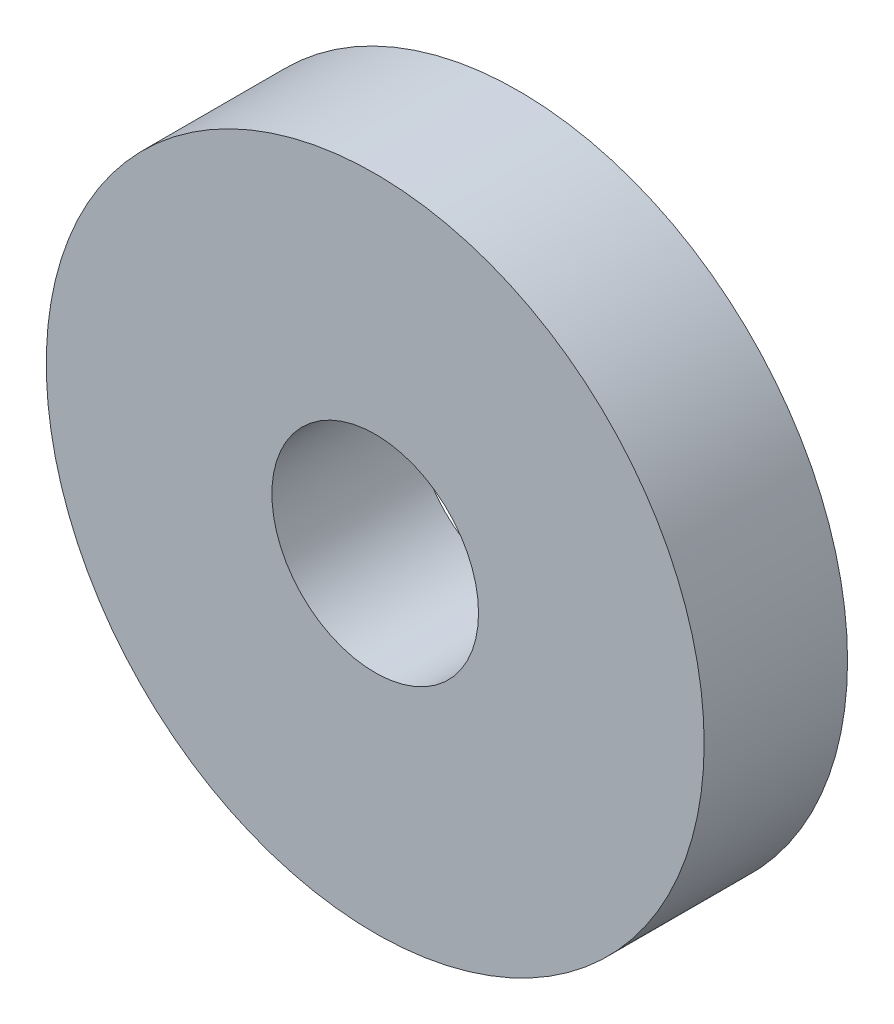
SolidWorks part; units mm, degrees
ref_plane "Front Plane" through (0, 0, 0) normal (0, 0, 1) x (1, 0, 0)
ref_plane "Top Plane" through (0, 0, 0) normal (0, 1, 0) x (1, 0, 0)
ref_plane "Right Plane" through (0, 0, 0) normal (1, 0, 0) x (0, 0, -1)
sketch "Sketch1" plane through (0, 0, 0) normal (0, 0, 1) x (1, 0, 0)
  circle A0 centre (0, 0) radius 1.2446
  circle A1 centre (0, 0) radius 3.9624
  dimension "ID" = 2.4892
  dimension "OD" = 7.9248
extrude "Extrude1" add sketch "Sketch1" against normal blind 1.7272
